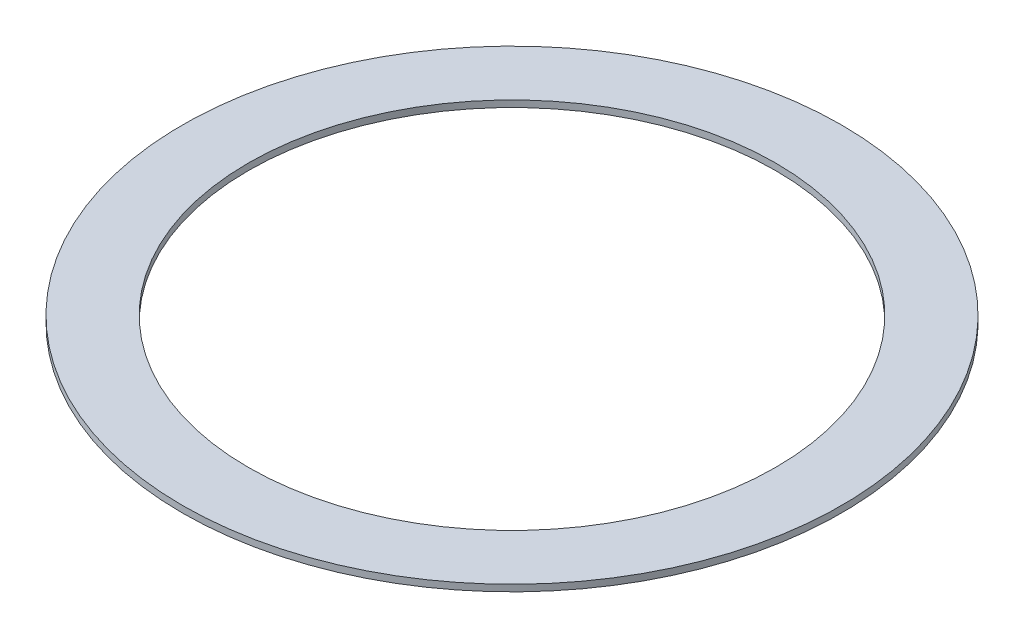
SolidWorks part; units mm, degrees
ref_plane "Alzado" through (0, 0, 0) normal (0, 0, 1) x (1, 0, 0)
ref_plane "Planta" through (0, 0, 0) normal (0, 1, 0) x (1, 0, 0)
ref_plane "Vista lateral" through (0, 0, 0) normal (1, 0, 0) x (0, 0, -1)
sketch "Croquis1" plane through (0, 0, 0) normal (0, 1, 0) x (1, 0, 0)
  circle A0 centre (0, 0) radius 100
  circle A1 centre (0, 0) radius 80
  dimension "D1" = 200
  dimension "D2" = 160
extrude "Saliente-Extruir1" add sketch "Croquis1" along normal blind 2
